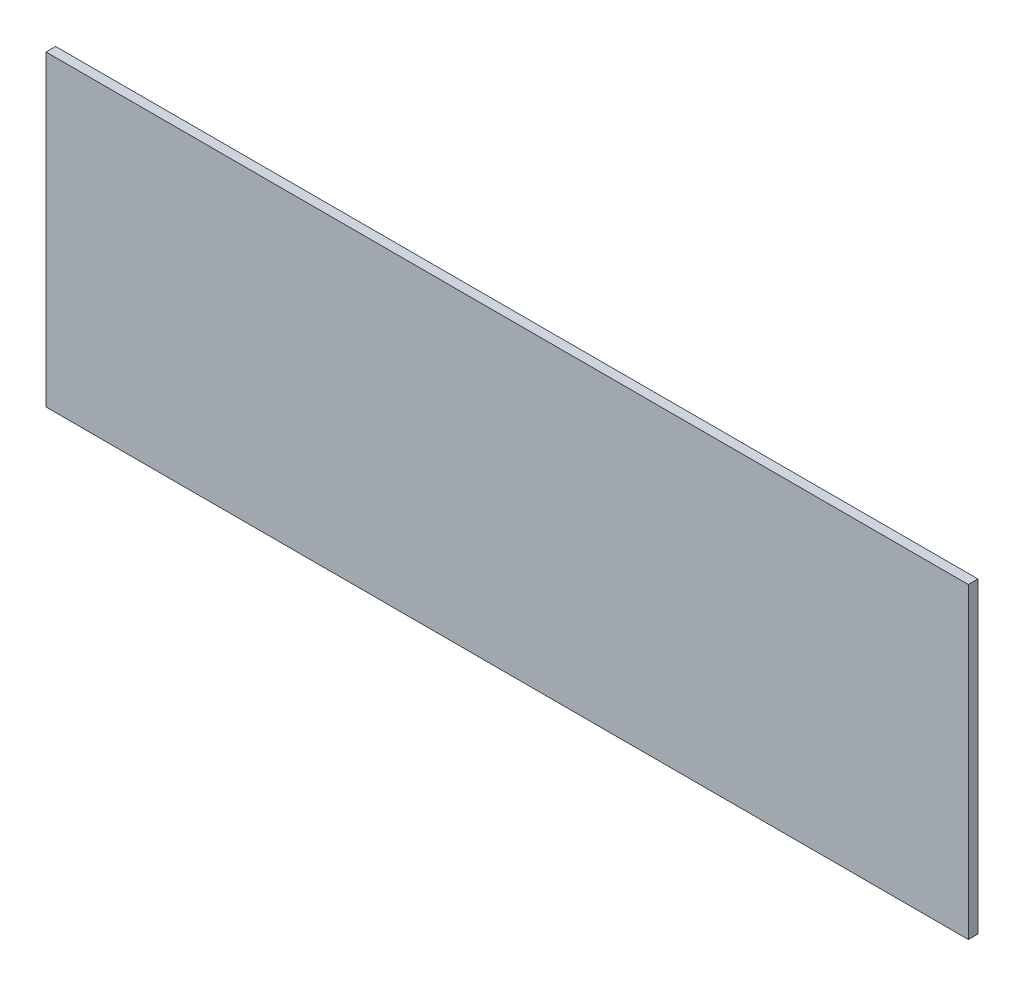
SolidWorks part; units mm, degrees
ref_plane "Front Plane" through (0, 0, 0) normal (0, 0, 1) x (1, 0, 0)
ref_plane "Top Plane" through (0, 0, 0) normal (0, 1, 0) x (1, 0, 0)
ref_plane "Right Plane" through (0, 0, 0) normal (1, 0, 0) x (0, 0, -1)
sketch "Sketch1" plane through (0, 0, 0) normal (0, 0, 1) x (1, 0, 0)
  line L1 (-152.4, -50.8) -> (152.4, -50.8)
  line L2 (-152.4, -50.8) -> (-152.4, 50.8)
  line L3 (-152.4, 50.8) -> (152.4, 50.8)
  line L4 (152.4, -50.8) -> (152.4, 50.8)
  line L5 (-152.4, -50.8) -> (152.4, 50.8) construction
  line L6 (-152.4, 50.8) -> (152.4, -50.8) construction
  point P0 (0, 0)
  dimension "D1" = 304.8
  dimension "D2" = 101.6
extrude "Boss-Extrude1" add sketch "Sketch1" along normal blind 3.175
